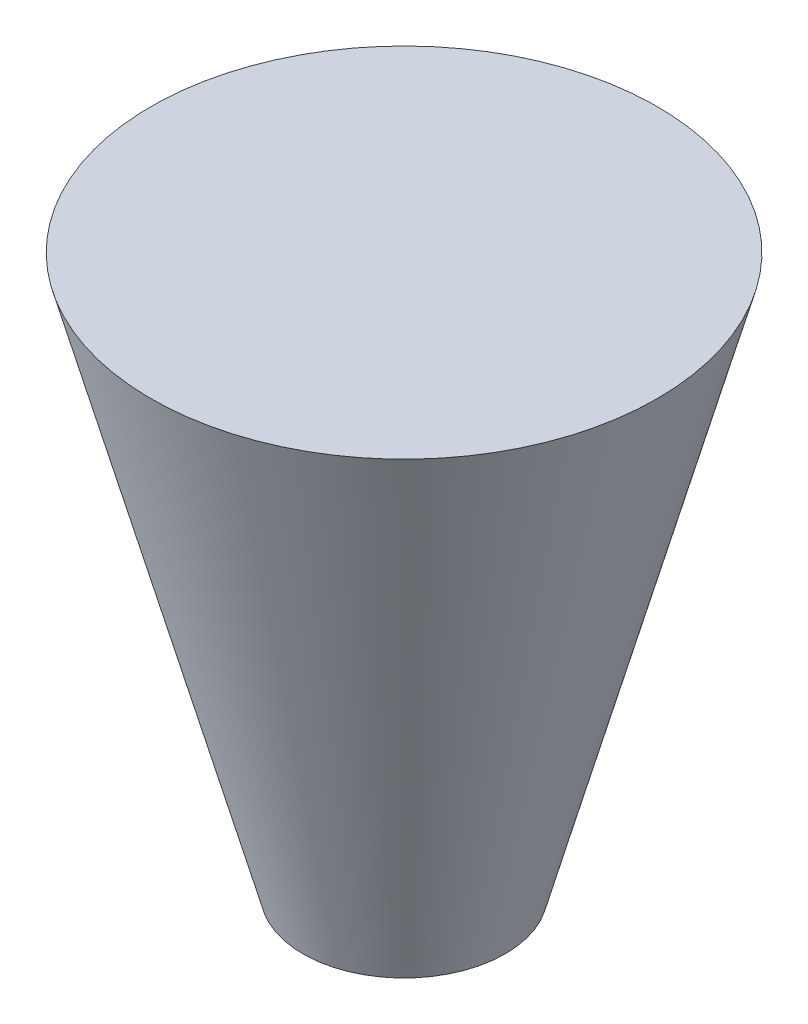
SolidWorks part; units mm, degrees
ref_plane "Front Plane" through (0, 0, 0) normal (0, 0, 1) x (1, 0, 0)
ref_plane "Top Plane" through (0, 0, 0) normal (0, 1, 0) x (1, 0, 0)
ref_plane "Right Plane" through (0, 0, 0) normal (1, 0, 0) x (0, 0, -1)
sketch "Sketch1" plane through (0, 0, 0) normal (0, 0, 1) x (1, 0, 0)
  line L0 (0, 0) -> (0, 74.9108) construction
  line L1 (0, 74.9108) -> (0, -83.8191) construction
  line L2 (0, -50) -> (-20, -50)
  line L3 (-20, -50) -> (-50, 60)
  line L4 (-50, 60) -> (0, 60)
  line L5 (0, -50) -> (0, 60)
  dimension "D1" = 50
  dimension "D2" = 110
  dimension "D3" = 20
  dimension "D4" = 50
revolve "Revolve1" add sketch "Sketch1" angle 360 about L5
